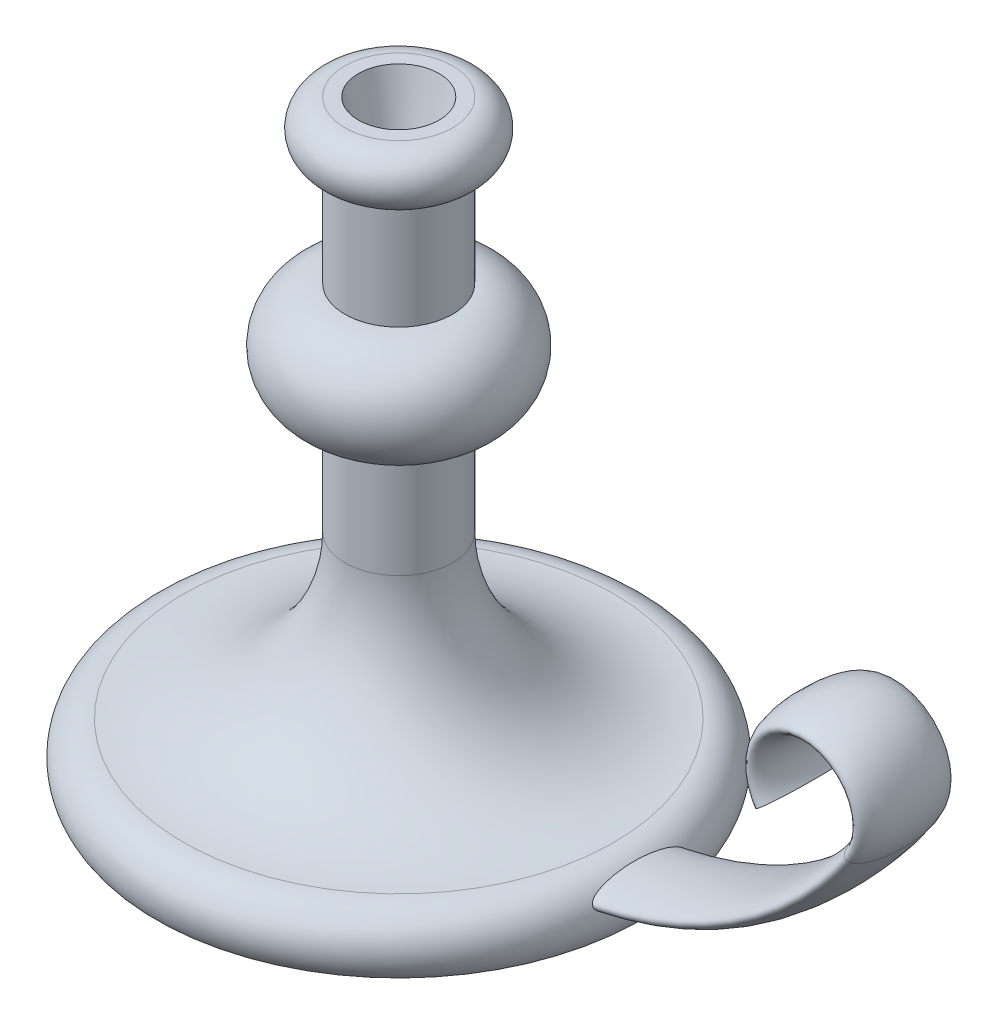
SolidWorks part; units mm, degrees
ref_plane "Front Plane" through (0, 0, 0) normal (0, 0, 1) x (1, 0, 0)
ref_plane "Top Plane" through (0, 0, 0) normal (0, 1, 0) x (1, 0, 0)
ref_plane "Right Plane" through (0, 0, 0) normal (1, 0, 0) x (0, 0, -1)
sketch "Sketch1" plane through (0, 0, 0) normal (0, 0, 1) x (1, 0, 0)
  line L0 (0, 0) -> (0, 220)
  line L1 (0, 220) -> (20, 220)
  line L2 (0, 0) -> (90, 0)
  line L3 (20, 200) -> (20, 160)
  line L4 (20, 120) -> (20, 80)
  arc A0 (20, 220) -> (20, 200) centre (20, 210) cw
  arc A1 (20, 160) -> (20, 120) centre (20, 140) cw
  arc A2 (20, 80) -> (80, 20) centre (80, 80) ccw
  arc A3 (80, 20) -> (90, 0) centre (80, 7.5) cw
  dimension "D4" = 10
  dimension "D5" = 20
  dimension "D8" = 60
  dimension "D9" = 12.5
  dimension "D1" = 220
  dimension "D2" = 90
  dimension "D3" = 20
  dimension "D6" = 40
  dimension "D7" = 80
revolve "Revolve1" add sketch "Sketch1" angle 360 about L0
sketch "Sketch2" plane through (0, 0, 0) normal (0, 0, 1) x (1, 0, 0)
  line L0 (0, 10) -> (60, 10)
  line L1 (0, 227.4356) -> (0, 175.1288) construction
  arc A0 (60, 10) -> (183.5921, 75) centre (60, 160) ccw
  arc A1 (183.5921, 75) -> (150.6342, 75) centre (167.1131, 86.3333) ccw
  dimension "D3" = 150
  dimension "D4" = 20
  dimension "D1" = 60
  dimension "D2" = 65
  dimension "D5" = 10
sketch "Sketch3" plane through (0, 0, 0) normal (1, 0, 0) x (0, 0, -1)
  line L0 (0, 126.8188) -> (0, -13.6376) construction
  ellipse E0 centre (0, 10) end of major axis (17.5, 10) minor radius 5
  dimension "D1" = 10
  dimension "D2" = 35
sweep "Sweep1" add profiles "Sketch3" path "Sketch2"
sketch "Sketch4" plane through (0, 220, 0) normal (0, 1, 0) x (1, 0, 0)
  circle A0 centre (0, 0) radius 15
  dimension "D1" = 30
extrude "Cut-Extrude1" cut sketch "Sketch4" against normal blind 25 draft 15
